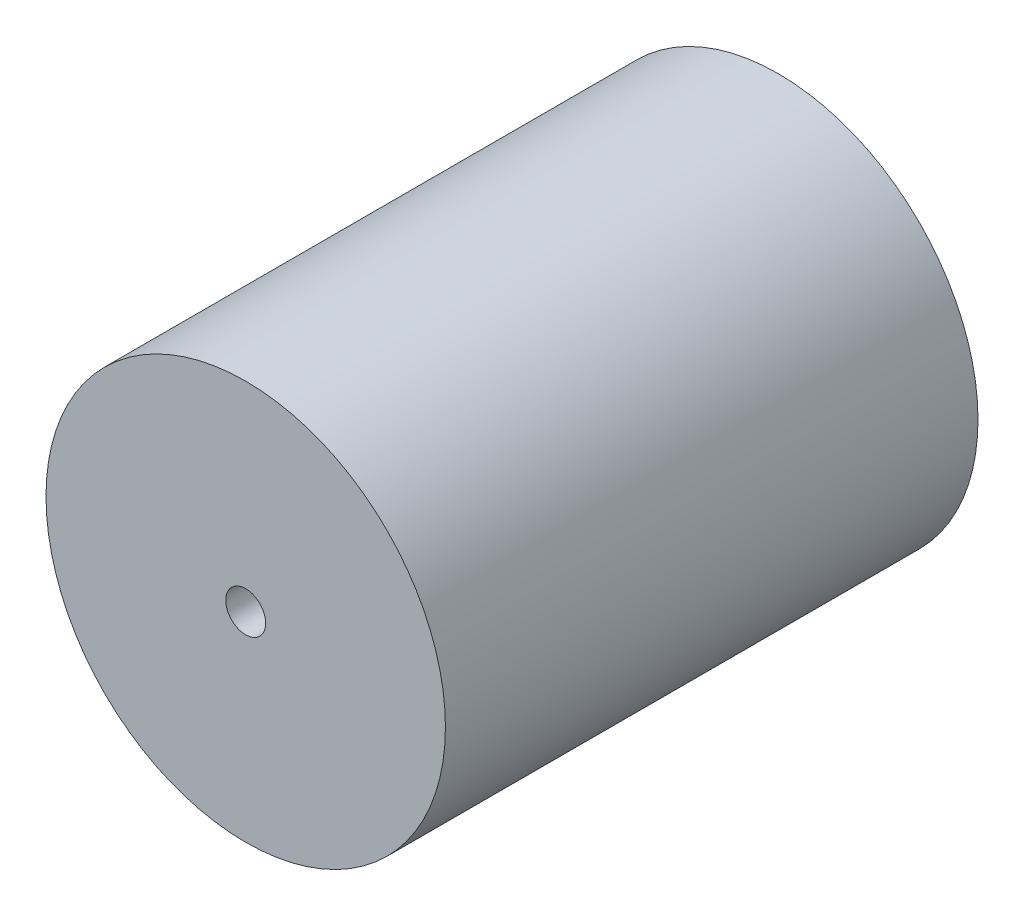
SolidWorks part; units mm, degrees
ref_plane "Alzado" through (0, 0, 0) normal (0, 0, 1) x (1, 0, 0)
ref_plane "Planta" through (0, 0, 0) normal (0, 1, 0) x (1, 0, 0)
ref_plane "Vista lateral" through (0, 0, 0) normal (1, 0, 0) x (0, 0, -1)
sketch "Croquis1" plane through (0, 0, 0) normal (0, 0, 1) x (1, 0, 0)
  circle A0 centre (0, 0) radius 15
  circle A1 centre (0, 0) radius 1.5
  dimension "D1" = 30
  dimension "D2" = 3
extrude "Saliente-Extruir1" add sketch "Croquis1" along normal blind 40
